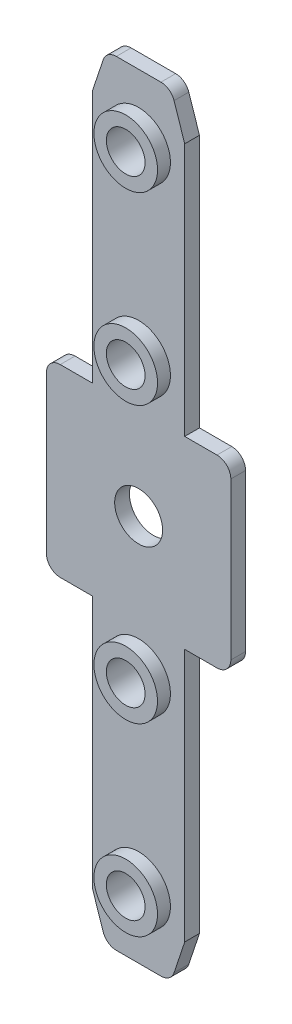
SolidWorks part; units mm, degrees
material "Plain Carbon Steel"
ref_plane "Front Plane" through (0, 0, 0) normal (0, 0, 1) x (1, 0, 0)
ref_plane "Top Plane" through (0, 0, 0) normal (0, 1, 0) x (1, 0, 0)
ref_plane "Right Plane" through (0, 0, 0) normal (1, 0, 0) x (0, 0, -1)
sketch "Sketch1" plane through (0, 0, 0) normal (0, 0, 1) x (1, 0, 0)
  line L0 (-10, 0) -> (0, 0) construction
  line L1 (0, 0) -> (0, 41.985) construction
  line L2 (-10, -8.5) -> (-10, 8.5)
  line L3 (-8.5, 10) -> (-5, 10)
  line L4 (-5, 10) -> (-5, 37.485)
  line L5 (-5, 37.485) -> (-3.8419, 40.9593)
  line L6 (-2.4189, 41.985) -> (2.4189, 41.985)
  line L7 (5, 37.485) -> (3.8419, 40.9593)
  line L8 (5, 10) -> (5, 37.485)
  line L9 (8.5, 10) -> (5, 10)
  line L10 (10, -8.5) -> (10, 8.5)
  line L11 (8.5, -10) -> (5, -10)
  line L12 (5, -10) -> (5, -37.485)
  line L13 (5, -37.485) -> (3.8419, -40.9593)
  line L14 (-2.4189, -41.985) -> (2.4189, -41.985)
  line L15 (-5, -37.485) -> (-3.8419, -40.9593)
  line L16 (-5, -10) -> (-5, -37.485)
  line L17 (-8.5, -10) -> (-5, -10)
  circle A0 centre (0, 0) radius 2.6
  arc A1 (-2.4189, -41.985) -> (-3.8419, -40.9593) centre (-2.4189, -40.485) cw
  arc A2 (3.8419, -40.9593) -> (2.4189, -41.985) centre (2.4189, -40.485) cw
  arc A3 (-3.8419, 40.9593) -> (-2.4189, 41.985) centre (-2.4189, 40.485) cw
  arc A4 (3.8419, 40.9593) -> (2.4189, 41.985) centre (2.4189, 40.485) ccw
  arc A5 (-8.5, -10) -> (-10, -8.5) centre (-8.5, -8.5) cw
  arc A6 (-10, 8.5) -> (-8.5, 10) centre (-8.5, 8.5) cw
  arc A7 (8.5, 10) -> (10, 8.5) centre (8.5, 8.5) cw
  arc A8 (8.5, -10) -> (10, -8.5) centre (8.5, -8.5) ccw
  point P15 (10, 0)
  point P24 (-3.5, -41.985)
  point P27 (3.5, -41.985)
  point P30 (-3.5, 41.985)
  point P33 (3.5, 41.985)
  point P36 (-10, -10)
  point P39 (-10, 10)
  point P42 (10, 10)
  point P45 (10, -10)
  dimension "D4" = 5.2
  dimension "D8" = 1.5
  dimension "D1" = 20
  dimension "D2" = 20
  dimension "D3" = 10
  dimension "D5" = 4.5
  dimension "D6" = 83.97
  dimension "D7" = 7
extrude "Boss-Extrude1" add sketch "Sketch1" along normal blind 1.6
sketch "Sketch2" plane through (0, 0, 1.6) normal (0, 0, 1) x (1, 0, 0)
  line L0 (-10, 0) -> (0, 0) construction
  line L1 (-10, 8.5) -> (-10, -8.5) construction
  line L2 (0, 0) -> (0, 41.985) construction
  line L3 (2.4189, 41.985) -> (-2.4189, 41.985) construction
  circle A0 centre (0, 14.95) radius 3.45
  circle A1 centre (0, 34.95) radius 3.45
  circle A2 centre (0, -14.95) radius 3.45
  circle A3 centre (0, -34.95) radius 3.45
  dimension "D1" = 6.9
  dimension "D3" = 14.95
  dimension "D2" = 20
extrude "Boss-Extrude2" add sketch "Sketch2" along normal blind 1.4
hole_wizard "M5x0.8 Tapped Hole1" positions "Sketch4" profile "Sketch3" tap size "M5x0.8" standard "ANSI Metric" end condition through all
sketch "Sketch4" plane through (0, 0, 3) normal (0, 0, 1) x (1, 0, 0)
  point P0 (0, 34.95)
  point P3 (0, 14.95)
  point P6 (0, -14.95)
  point P9 (0, -34.95)
sketch "Sketch3" plane through (0, 34.95, 3) normal (1, 0, 0) x (0, -1, 0)
  line L0 (0, 0) -> (0, 3)
  line L1 (0, 3) -> (2.1, 3)
  line L2 (2.1, 3) -> (2.1, 0)
  line L5 (2.1, 0) -> (0, 0)
  line L11 (0, -6.35) -> (0, 107.95) construction
  dimension "Thru Tap Drill Dia." = 4.2
  dimension "Thru Tap Drill Depth" = 3
cosmetic thread "Hole Thread1" parameters "D2"=5
cosmetic thread "Hole Thread2" parameters "D2"=5
cosmetic thread "Hole Thread3" parameters "D2"=5
cosmetic thread "Hole Thread4" parameters "D2"=5
